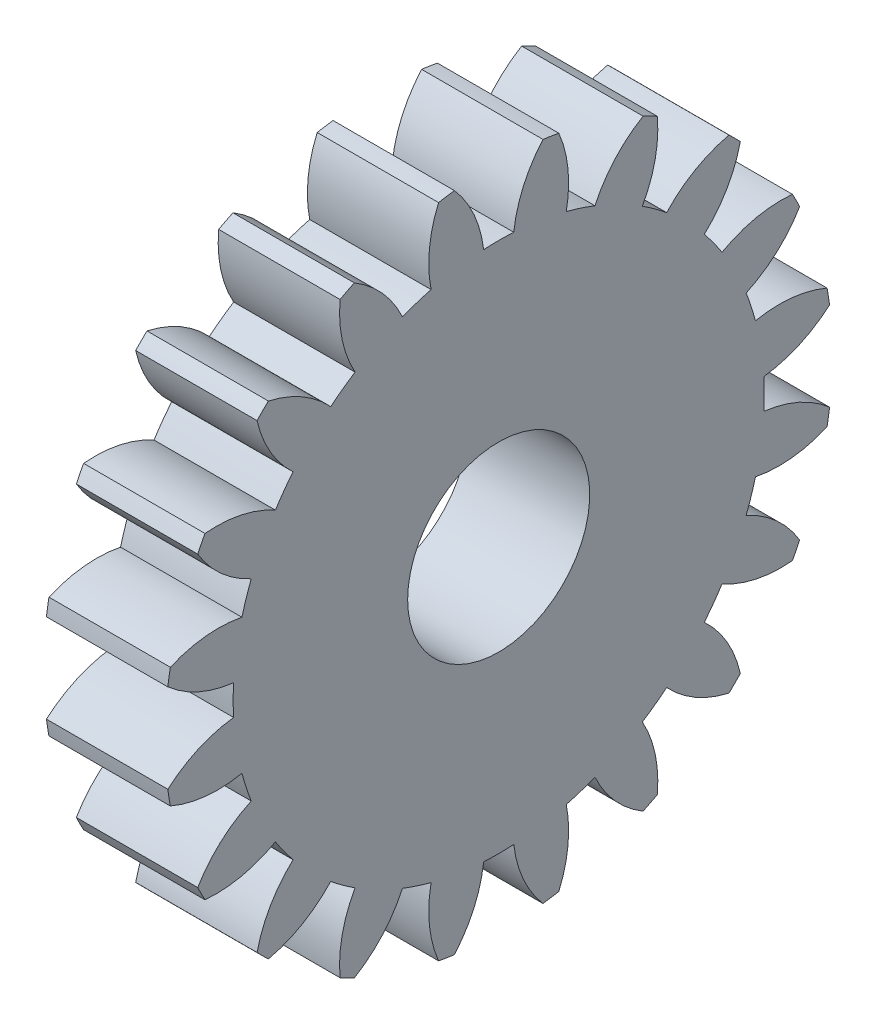
SolidWorks part; units mm, degrees
ref_plane "Plane1" through (0, 0, 0) normal (0, 0, 1) x (1, 0, 0)
ref_plane "Plane2" through (0, 0, 0) normal (0, 1, 0) x (1, 0, 0)
ref_plane "Plane3" through (0, 0, 0) normal (1, 0, 0) x (0, 0, -1)
sketch "HoldingSke" plane through (0, 0, 0) normal (0, 1, 0) x (1, 0, 0)
  line L0 (0, 0) -> (0.6265, -0.228)
  line L1 (-15, 0) -> (100, 0) construction
  line L2 (0, 0) -> (-2.1039, 2.3779)
  line L3 (0, 0) -> (-11.863, 4.5341)
  line L4 (0, 0) -> (8.1152, 2.9537)
  line L5 (0, 0) -> (-46.8476, -17.4728)
  line L6 (0, 0) -> (-4.9738, -3.3558)
  line L7 (-2.1039, 2.3779) -> (8.6586, 51.2059)
  line L8 (-76.2, 54.61) -> (-74.8, 54.61)
  line L9 (-71.009, 38.7566) -> (-53.1078, 45.2721)
  line L10 (-76.2, 71.12) -> (104.1128, 71.12)
  line L11 (0, 0) -> (-6, 0)
  line L12 (-76.2, 101.6) -> (-76.147, 101.6)
  line L13 (24.9733, 27.94) -> (52.9518, 28.4284)
  line L14 (24.9733, 27.94) -> (24.9743, 27.94)
  line L15 (24.9733, 27.94) -> (100.4006, 29.5858)
  line L16 (-63.627, -1.5) -> (-12.827, -1.5)
  circle A0 centre (0, 0) radius 4.5
  circle A1 centre (0, 0) radius 13.124
  circle A2 centre (0, 0) radius 37.5
  circle A3 centre (0, 0) radius 4.5
  dimension "MHD" = 26.248
  dimension "Hub_dia" = 75
  dimension "Bore" = 9
  dimension "MBD" = 9
  dimension "Num_teeth" = 20
  dimension "Pitch" = 0.6667
  dimension "Overall_len" = 50
  dimension "Show_teeth" = 20
  dimension "Thickness" = 6
  dimension "OAL" = 50.0001
  dimension "T_dim" = 1.4
  dimension "Ap" = 20
  dimension "H" = 19.05
  dimension "Pitch_radius" = 180.3128
  dimension "Width" = 6
  dimension "Backlash" = 0.053
  dimension "Addendum_fac" = 1
  dimension "Dedendum_fac" = 1.25
  dimension "Clearance_fac" = 0.25
  dimension "Dedendum_add" = 0.001
  dimension "Module" = 1.5
sketch "BasProSke" plane through (0, 0, 0) normal (0, 1, 0) x (1, 0, 0)
  line L0 (-10, 0) -> (60, 0) construction
  line L1 (0, 0) -> (0, 16.5)
  line L2 (0, 0) -> (6, 0)
  line L3 (6, 0) -> (6, 16.5)
  line L4 (6, 16.5) -> (0, 16.5)
  dimension "Thickness" = 6
  dimension "Diameter" = 33
revolve "Base-Revolve" add sketch "BasProSke" angle 360 about L0
sketch "TooCutSke" plane through (0, 0, 0) normal (1, 0, 0) x (0, 0, -1)
  line L1 (0, 0) -> (0, 107) construction
  line L2 (0, 0) -> (-1.2696, 14.9462) construction
  line L3 (0, 0) -> (-4.6808, 29.5532) construction
  line L4 (-1.2696, 14.9462) -> (-2.3404, 14.7766) construction
  arc A0 (0.7438, 13.1029) -> (-0.7438, 13.1029) centre (0, 0) ccw
  arc A1 (2.21, 16.377) -> (-2.21, 16.377) centre (0, 0) ccw
  circle A2 centre (0, 0) radius 15 construction
  circle A3 centre (0, 0) radius 14.0954 construction
  arc A4 (-0.7438, 13.1029) -> (-2.21, 16.377) centre (-6.7025, 12.3999) ccw
  arc A5 (2.21, 16.377) -> (0.7438, 13.1029) centre (6.7025, 12.3999) ccw
  dimension "Root_dia" = 26.248
  dimension "Overcut_dia" = 33.0508
  dimension "Pitch_dia" = 30
  dimension "Base_dia" = 28.1908
  dimension "Flank_rad" = 6
  dimension "Half_ang" = 9
  dimension "Half_CT" = 1.0841
extrude "ToothCut" cut sketch "TooCutSke" along normal through all
fillet "Breaks" [suppressed] radius 0.03
fillet "RootFillets" [suppressed] radius 0.376
pattern_circular "TeethCuts" count 20 every 18 about axis through (-10, 0, 0) along (1, 0, 0) of "ToothCut", "RootFillets", "Breaks"
sketch "HubNeaOneSke" plane through (0, 0, 0) normal (-1, 0, 0) x (0, 0, 1)
  circle A0 centre (0, 0) radius 13.124
  dimension "Diameter" = 26.248
extrude "HubNearOne" [suppressed] add sketch "HubNeaOneSke" along normal blind 44.0001
sketch "HubNeaBotSke" plane through (0, 0, 0) normal (-1, 0, 0) x (0, 0, 1)
  circle A0 centre (0, 0) radius 13.124
  dimension "Diameter" = 26.248
extrude "HubNearBoth" [suppressed] add sketch "HubNeaBotSke" along normal blind 22
ref_plane "FarPln" through (6, 0, 0) normal (1, 0, 0) x (0, 0, -1)
sketch "HubFarSke" plane through (6, 0, 0) normal (1, 0, 0) x (0, 0, -1)
  circle A0 centre (0, 0) radius 13.124
  dimension "Diameter" = 26.248
extrude "HubFar" [suppressed] add sketch "HubFarSke" along normal blind 22
sketch "BorSke" plane through (0, 0, 0) normal (1, 0, 0) x (0, 0, -1)
  circle A0 centre (0, 0) radius 4.5
  dimension "Diameter" = 9
extrude "Bore" cut sketch "BorSke" along normal mid plane 100.0001
sketch "KeySke" plane through (0, 0, 0) normal (1, 0, 0) x (0, 0, -1)
  line L0 (-1.5, 0) -> (-1.5, 5.9)
  line L1 (-1.5, 5.9) -> (1.5, 5.9)
  line L2 (1.5, 5.9) -> (1.5, 0)
  line L3 (0, 0) -> (0, 34) construction
  line L4 (-1.5, 0) -> (1.5, 0)
  dimension "Offset" = 5.9
  dimension "Width" = 3
extrude "Keyway" [suppressed] cut sketch "KeySke" along normal mid plane 100.0001
pattern_circular "Keyway2" [suppressed] count 2 every 90 about axis through (-10, 0, 0) along (1, 0, 0)
sketch "Esquisse1" plane through (6, 0, 0) normal (1, 0, 0) x (0, 0, -1)
  circle A0 centre (0, 0) radius 15
  dimension "D1" = 30
equation "' \"Module@HoldingSke\" = 6.35"
equation "' \"Num_teeth@HoldingSke\" = 12"
equation "' \"Ap@HoldingSke\" =  20"
equation "' \"Ap@HoldingSke\" = 20"
equation "' \"Width@HoldingSke\" = 0.5 * 25.4"
equation "' \"Hub_dia@HoldingSke\"= 1 * 25.4"
equation "' \"Hub_dia@HoldingSke\" = 1 * 25.4"
equation "' \"Overall_len@HoldingSke\" = 1.0 * 25.4"
equation "' \"Bore@HoldingSke\" = 0.75 * 25.4"
equation "' \"T_dim@HoldingSke\" = 0.1 * 25.4"
equation "' \"Width@KeySke\" = 0.25 * 25.4"
equation "' \"Show_teeth@HoldingSke\" = 13"
equation "' \"Backlash@HoldingSke\" = 0.009 * 25.4"
equation "' \"Addendum_fac@HoldingSke\" = 1.0"
equation "' \"Dedendum_fac@HoldingSke\" = 1.25"
equation "' \"Dedendum_add@HoldingSke\" = 0.00005 * 25.4"
equation "' \"Clearance_fac@HoldingSke\" = 0.25"
equation "\"Pitch@HoldingSke\" = 1 / \"Module@HoldingSke\""
equation "\"Overcut_dia@TooCutSke\" = (\"Num_teeth@HoldingSke\" + 2 * \"Addendum_fac@HoldingSke\") / \"Pitch@HoldingSke\" + 0.002 * 25.4"
equation "\"Pitch_dia@TooCutSke\" = \"Num_teeth@HoldingSke\" / \"Pitch@HoldingSke\""
equation "\"Base_dia@TooCutSke\" = \"Num_teeth@HoldingSke\" / \"Pitch@HoldingSke\" * cos((\"Ap@HoldingSke\"  * 3.14159265 / 180))"
equation "\"Root_dia@TooCutSke\" = (\"Num_teeth@HoldingSke\" + 2) / \"Pitch@HoldingSke\" - 2 * (\"Addendum_fac@HoldingSke\" + \"Dedendum_fac@HoldingSke\") / \"Pitch@HoldingSke\" - \"Dedendum_add@HoldingSke\" * 2"
equation "\"Half_ang@TooCutSke\" = 180 / \"Num_teeth@HoldingSke\""
equation "\"Half_CT@TooCutSke\" = \"Num_teeth@HoldingSke\" / \"Pitch@HoldingSke\" * sin((3.14159265 / 2 / \"Num_teeth@HoldingSke\")) / 2 - 7 * \"Backlash@HoldingSke\" / 4"
equation "\"Flank_rad@TooCutSke\" = \"Num_teeth@HoldingSke\" / \"Pitch@HoldingSke\" / 5"
equation "\"Radius@RootFillets\" = \"Clearance_fac@HoldingSke\" / \"Pitch@HoldingSke\" + \"Dedendum_add@HoldingSke\""
equation "\"Break_rad@Breaks\" = 0.02 / \"Pitch@HoldingSke\""
equation "\"Thickness@HoldingSke\" = \"Width@HoldingSke\""
equation "\"OAL@HoldingSke\" = \"Thickness@HoldingSke\""
equation "\"MHD@HoldingSke\" = (\"Num_teeth@HoldingSke\" + 2) / \"Pitch@HoldingSke\" - 2 * (\"Addendum_fac@HoldingSke\" + \"Dedendum_fac@HoldingSke\")  / \"Pitch@HoldingSke\" - \"Dedendum_add@HoldingSke\" * 2"
equation "\"MBD@HoldingSke\" = (\"Num_teeth@HoldingSke\" + 2) / \"Pitch@HoldingSke\" - 2 * (\"Addendum_fac@HoldingSke\" + \"Dedendum_fac@HoldingSke\")  / \"Pitch@HoldingSke\" - \"Dedendum_add@HoldingSke\" * 2 - 0.002 * 25.4"
equation "\"MHD@HoldingSke\" = ((sgn( \"MHD@HoldingSke\" - \"Hub_dia@HoldingSke\" )-1)*( \"MHD@HoldingSke\" - \"Hub_dia@HoldingSke\" ))/-2+ \"Hub_dia@HoldingSke\""
equation "\"MBD@HoldingSke\" = ((sgn( \"MBD@HoldingSke\" - \"Bore@HoldingSke\" )-1)*( \"MBD@HoldingSke\" - \"Bore@HoldingSke\" ))/-2+ \"Bore@HoldingSke\""
equation "\"OAL@HoldingSke\" = ((sgn( \"OAL@HoldingSke\" - \"Overall_len@HoldingSke\" )+1)*( \"OAL@HoldingSke\" - \"Overall_len@HoldingSke\" ))/2 + \"Overall_len@HoldingSke\" + 0.000002 * 25.4"
equation "\"Num_teeth@TeethCuts\" = int( \"Show_teeth@HoldingSke\" ) + 1"
equation "\"Num_teeth@TeethCuts\" = ((sgn( \"Num_teeth@TeethCuts\" - \"Num_teeth@HoldingSke\" )-1)*( \"Num_teeth@TeethCuts\" - \"Num_teeth@HoldingSke\" ))/-2+ \"Num_teeth@HoldingSke\""
equation "\"Num_teeth@TeethCuts\" = ((sgn( \"Num_teeth@TeethCuts\" - 2.0)+1)*( \"Num_teeth@TeethCuts\" - 2.0))/2 +2.0"
equation "\"Angle@TeethCuts\" = 360.0 / \"Num_teeth@HoldingSke\""
equation "\"Diameter@BasProSke\" = (\"Num_teeth@HoldingSke\" + 2 * \"Addendum_fac@HoldingSke\") / \"Pitch@HoldingSke\""
equation "\"Thickness@BasProSke\"  = \"Thickness@HoldingSke\""
equation "' \"Fillet_rad@BasProSke\" =  \"Thickness@HoldingSke\" * 0.05"
equation "' \"Fillet_rad@BasProSke\" = \"Thickness@HoldingSke\" * 0.05"
equation "\"MHD@HoldingSke\" = ((sgn( \"MHD@HoldingSke\" - \"Root_dia@TooCutSke\" )-1)*( \"MHD@HoldingSke\" - \"Root_dia@TooCutSke\" ))/-2+ \"Root_dia@TooCutSke\""
equation "\"Diameter@HubNeaOneSke\" = \"MHD@HoldingSke\""
equation "\"Length@HubNearOne\" = \"OAL@HoldingSke\" - \"Thickness@BasProSke\""
equation "\"Diameter@HubNeaBotSke\" = \"MHD@HoldingSke\""
equation "\"Length@HubNearBoth\" = ( \"OAL@HoldingSke\" - \"Thickness@BasProSke\" ) / 2.0"
equation "\"Thickness@FarPln\" = \"Thickness@BasProSke\""
equation "\"Diameter@HubFarSke\" = \"MHD@HoldingSke\""
equation "\"Length@HubFar\" = ( \"OAL@HoldingSke\" - \"Thickness@BasProSke\" ) / 2.0"
equation "\"Diameter@BorSke\" = \"MBD@HoldingSke\""
equation "\"D1@Bore\" = \"OAL@HoldingSke\" * 2.0"
equation "\"D1@Keyway\" = \"OAL@HoldingSke\" * 2.0"
equation "\"Offset@KeySke\" = \"T_dim@HoldingSke\" + \"MBD@HoldingSke\" / 2.0"
